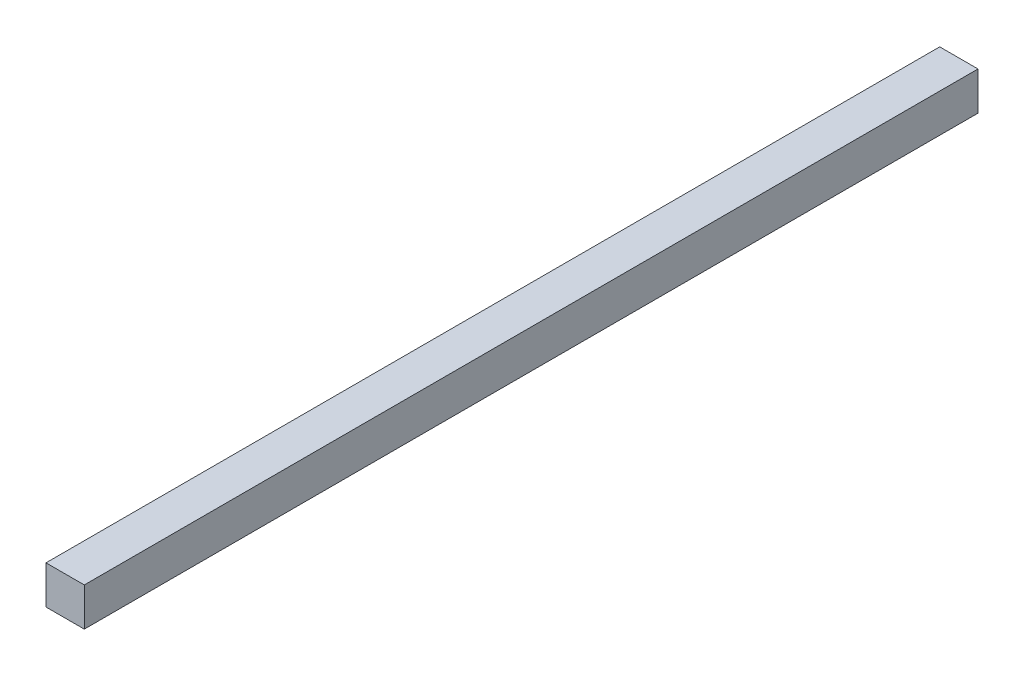
SolidWorks part; units mm, degrees
ref_plane "정면" through (0, 0, 0) normal (0, 0, 1) x (1, 0, 0)
ref_plane "윗면" through (0, 0, 0) normal (0, 1, 0) x (1, 0, 0)
ref_plane "우측면" through (0, 0, 0) normal (1, 0, 0) x (0, 0, -1)
sketch "스케치1" plane through (0, 0, 0) normal (0, 0, 1) x (1, 0, 0)
  line L1 (-15, -15) -> (15, -15)
  line L2 (-15, -15) -> (-15, 15)
  line L3 (-15, 15) -> (15, 15)
  line L4 (15, -15) -> (15, 15)
  line L5 (-15, -15) -> (15, 15) construction
  line L6 (-15, 15) -> (15, -15) construction
  point P0 (0, 0)
  dimension "D1" = 30
extrude "보스-돌출1" add sketch "스케치1" along normal blind 700
